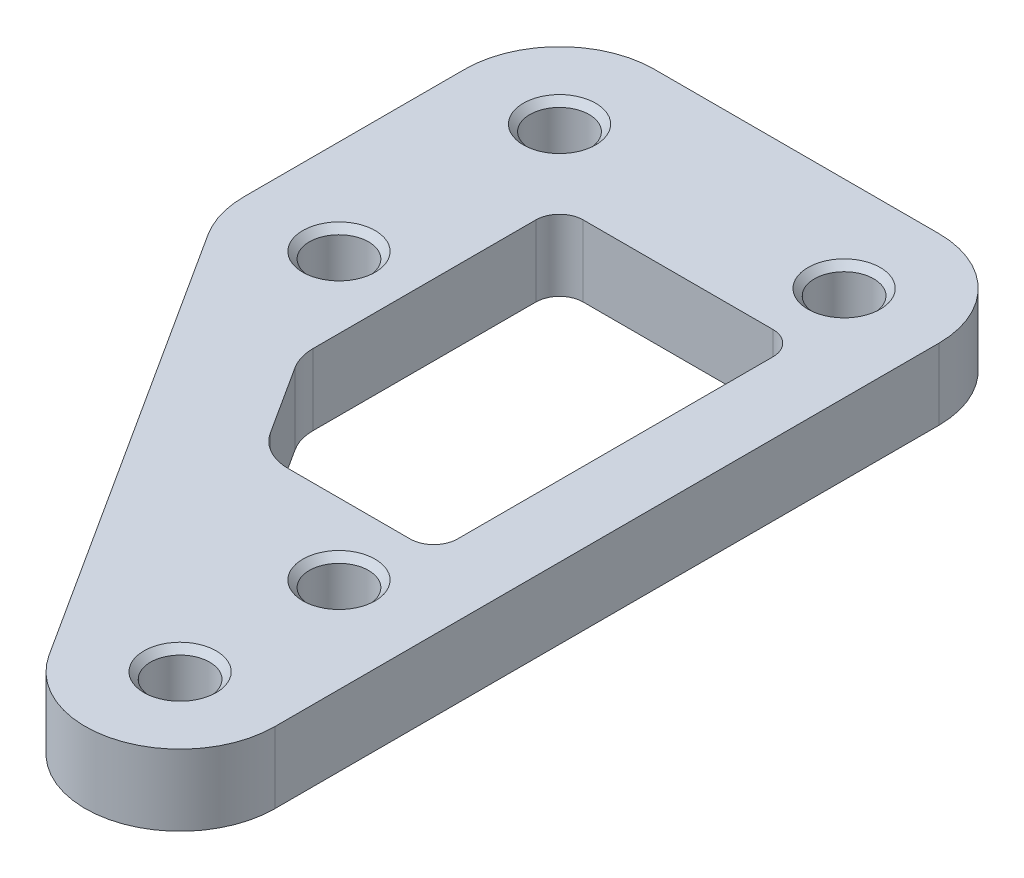
SolidWorks part; units mm, degrees
material "6061 合金"
ref_plane "前视基准面" through (0, 0, 0) normal (0, 0, 1) x (1, 0, 0)
ref_plane "上视基准面" through (0, 0, 0) normal (0, 1, 0) x (1, 0, 0)
ref_plane "右视基准面" through (0, 0, 0) normal (1, 0, 0) x (0, 0, -1)
sketch "草图1" plane through (0, 0, 0) normal (0, 1, 0) x (1, 0, 0)
  line L0 (4, -28) -> (4, 0)
  line L1 (0, -28) -> (0, 0) construction
  line L2 (-12, 0) -> (0, 0) construction
  line L3 (0, 4) -> (-12, 4)
  line L4 (-15.3665, -11.4603) -> (-3.3665, -30.1603)
  line L5 (-16, 0) -> (-16, -9.3)
  line L6 (-12, 0) -> (-12, -9.3) construction
  line L7 (-8.6832, -14.4686) -> (-6.8149, -17.3802)
  line L8 (-8, -3) -> (0, -3)
  line L9 (-9, -4) -> (-9, -13.3885)
  line L11 (1, -4) -> (1, -17.3)
  line L12 (0, -18.3) -> (-5.1316, -18.3)
  circle A0 centre (-12, 0) radius 1.5 construction
  circle A1 centre (0, 0) radius 1.5 construction
  circle A2 centre (0, -28) radius 1.5 construction
  circle A3 centre (0, -21.3) radius 1.5 construction
  circle A4 centre (-12, -9.3) radius 1.5 construction
  arc A5 (-15.3665, -11.4603) -> (-16, -9.3) centre (-12, -9.3) cw
  arc A6 (-3.3665, -30.1603) -> (4, -28) centre (0, -28) ccw
  arc A7 (0, 4) -> (4, 0) centre (0, 0) cw
  arc A8 (-12, 4) -> (-16, 0) centre (-12, 0) ccw
  arc A9 (0, -18.3) -> (1, -17.3) centre (0, -17.3) ccw
  arc A10 (0, -3) -> (1, -4) centre (0, -4) cw
  arc A11 (-8, -3) -> (-9, -4) centre (-8, -4) ccw
  arc A12 (-9, -13.3885) -> (-8.6832, -14.4686) centre (-7, -13.3885) ccw
  arc A13 (-6.8149, -17.3802) -> (-5.1316, -18.3) centre (-5.1316, -16.3) ccw
  dimension "D2" = 3
  dimension "D4" = 28
  dimension "D6" = 6.7
  dimension "D12" = 1
  dimension "D13" = 2
  dimension "D1" = 4
  dimension "D3" = 12
  dimension "D5" = 9.3
  dimension "D7" = 4
  dimension "D8" = 3
  dimension "D9" = 3
  dimension "D10" = 3
  dimension "D11" = 3
extrude "凸台-拉伸1" add sketch "草图1" along normal blind 3
hole_wizard "M3 螺纹孔1" positions "草图2" profile "草图3" tap size "M3" standard "GB" end condition through all
sketch "草图2" plane through (0, 3, 0) normal (0, 1, 0) x (1, 0, 0)
  point P0 (-12, 0)
  point P3 (-12, -9.3)
  point P6 (0, 0)
  point P9 (0, -21.3)
  point P12 (0, -28)
sketch "草图3" plane through (-12, 3, 0) normal (1, 0, 0) x (0, 0, 1)
  line L0 (0, 0) -> (0, 3)
  line L1 (0, 3) -> (1.25, 3)
  line L2 (1.25, 3) -> (1.25, 0.275)
  line L3 (1.25, 0.275) -> (1.525, 0)
  line L5 (1.525, 0) -> (0, 0)
  line L6 (-1.25, 0.275) -> (-1.525, 0) construction
  line L11 (0, -6.35) -> (0, 107.95) construction
  dimension "通孔螺纹孔钻头直径" = 2.5
  dimension "通孔螺纹孔钻头深度" = 3
  dimension "近端锥形沉头孔直径" = 3.05
  dimension "近端锥形沉头孔角度" = 90
cosmetic thread "孔螺蚊线1" parameters "D2"=3
cosmetic thread "孔螺蚊线2" parameters "D2"=3
cosmetic thread "孔螺蚊线3" parameters "D2"=3
cosmetic thread "孔螺蚊线4" parameters "D2"=3
cosmetic thread "孔螺蚊线5" parameters "D2"=3
